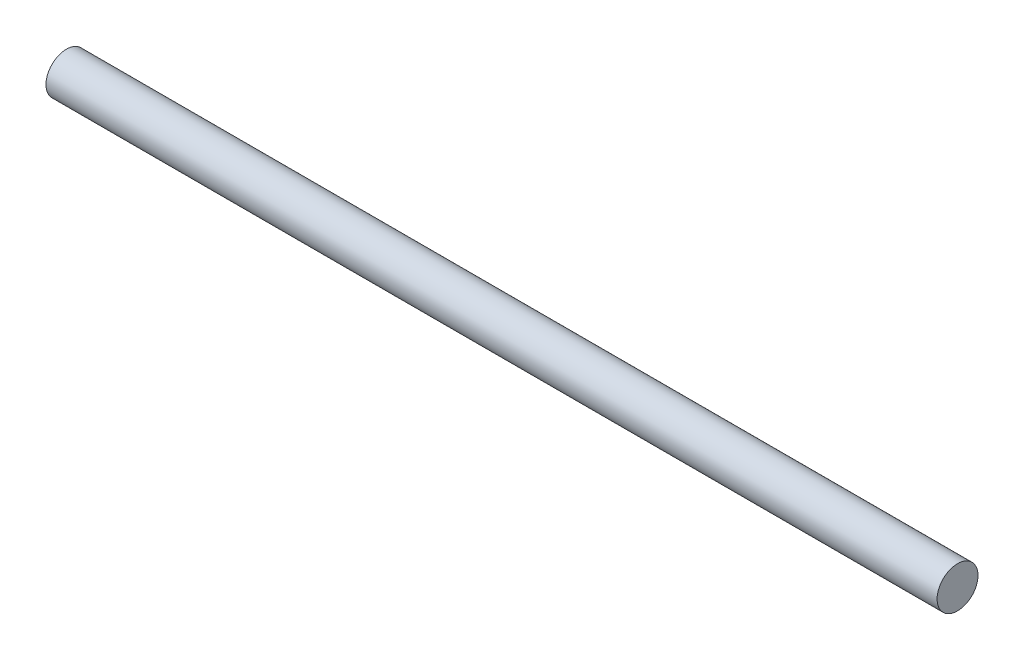
SolidWorks part; units mm, degrees
ref_plane "Front Plane" through (0, 0, 0) normal (0, 0, 1) x (1, 0, 0)
ref_plane "Top Plane" through (0, 0, 0) normal (0, 1, 0) x (1, 0, 0)
ref_plane "Right Plane" through (0, 0, 0) normal (1, 0, 0) x (0, 0, -1)
sketch "Sketch1" plane through (0, 0, 0) normal (1, 0, 0) x (0, 0, -1)
  circle A0 centre (0, 0) radius 2.2
  dimension "D1" = 4.4
extrude "Boss-Extrude1" add sketch "Sketch1" along normal mid plane 95.8
